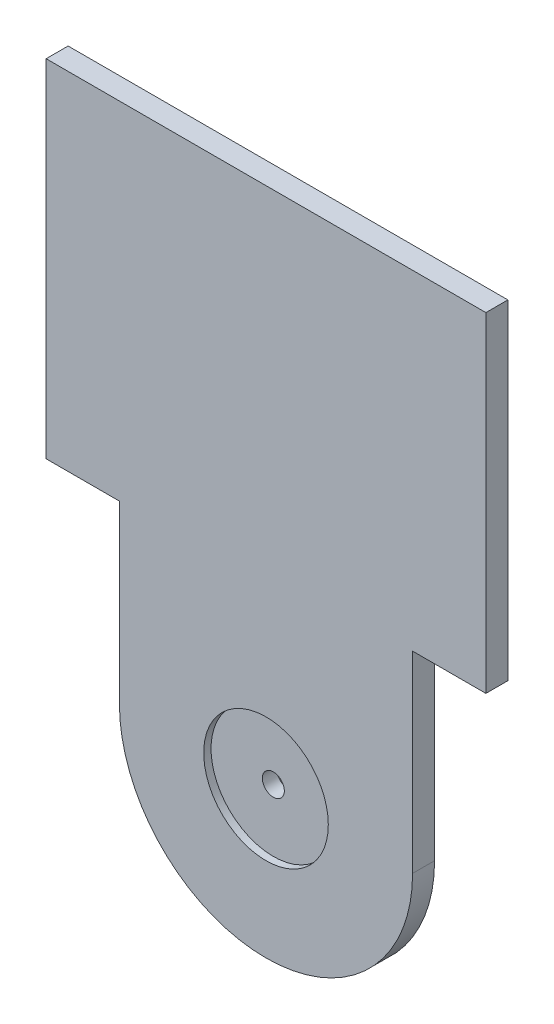
SolidWorks part; units mm, degrees
ref_plane "Alzado" through (0, 0, 0) normal (0, 0, 1) x (1, 0, 0)
ref_plane "Planta" through (0, 0, 0) normal (0, 1, 0) x (1, 0, 0)
ref_plane "Vista lateral" through (0, 0, 0) normal (1, 0, 0) x (0, 0, -1)
sketch "Croquis1" plane through (0, 0, 0) normal (0, 0, 1) x (1, 0, 0)
  line L0 (-113.9918, 10.9708) -> (-73.9918, 10.9708) construction
  line L1 (-113.9918, 10.9708) -> (-113.9918, 34.9581)
  line L2 (-113.9918, 34.9581) -> (-123.9918, 34.9581)
  line L3 (-123.9918, 34.9581) -> (-123.9918, 82.2366)
  line L4 (-123.9918, 82.2366) -> (-63.9918, 82.2366)
  line L5 (-73.9918, 10.9708) -> (-73.9918, 37.2366)
  line L6 (-73.9918, 37.2366) -> (-63.9918, 37.2366)
  line L7 (-63.9918, 37.2366) -> (-63.9918, 82.2366)
  arc A0 (-113.9918, 10.9708) -> (-73.9918, 10.9708) centre (-93.9918, 10.9708) ccw
  circle A1 centre (-93.9918, 10.9708) radius 1.5
  dimension "D6" = 3
  dimension "D3" = 60
  dimension "D4" = 10
  dimension "D5" = 10
  dimension "D8" = 45
extrude "Saliente-Extruir1" add sketch "Croquis1" along normal blind 3
sketch "Croquis2" plane through (0, 0, 3) normal (0, 0, 1) x (1, 0, 0)
  circle A0 centre (-93.9918, 10.9708) radius 8.5
extrude "Cortar-Extruir1" cut sketch "Croquis2" against normal blind 1
